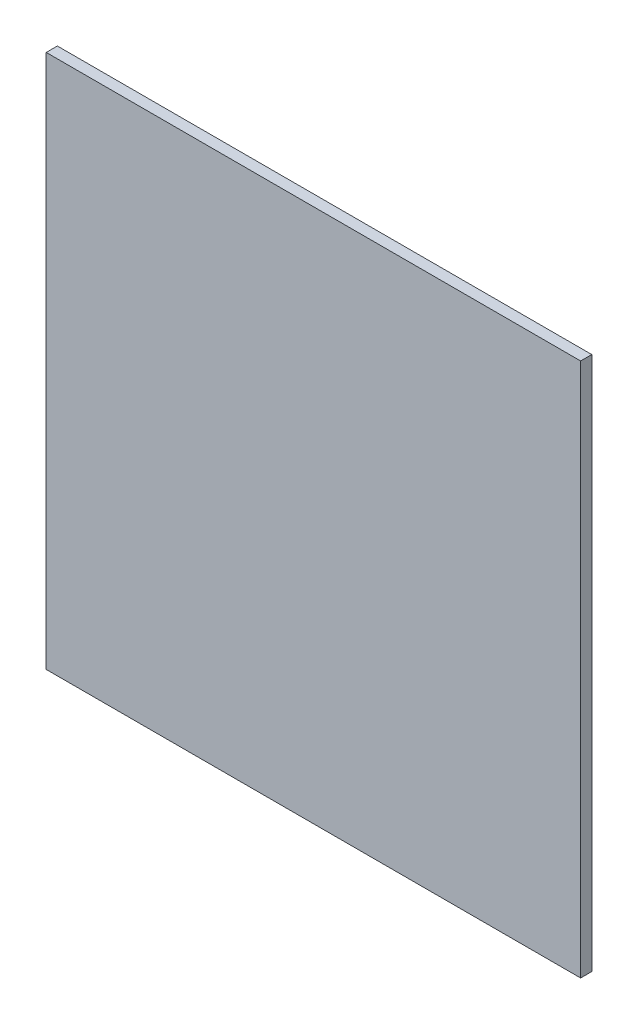
SolidWorks part; units mm, degrees
ref_plane "Front Plane" through (0, 0, 0) normal (0, 0, 1) x (1, 0, 0)
ref_plane "Top Plane" through (0, 0, 0) normal (0, 1, 0) x (1, 0, 0)
ref_plane "Right Plane" through (0, 0, 0) normal (1, 0, 0) x (0, 0, -1)
sketch "Sketch1" plane through (0, 0, 0) normal (0, 0, 1) x (1, 0, 0)
  line L1 (-304.8, -304.8) -> (304.8, -304.8)
  line L2 (-304.8, -304.8) -> (-304.8, 304.8)
  line L3 (-304.8, 304.8) -> (304.8, 304.8)
  line L4 (304.8, -304.8) -> (304.8, 304.8)
  line L5 (-304.8, -304.8) -> (304.8, 304.8) construction
  line L6 (-304.8, 304.8) -> (304.8, -304.8) construction
  point P0 (0, 0)
  dimension "D1" = 609.6
  dimension "D2" = 609.6
extrude "Boss-Extrude1" add sketch "Sketch1" along normal blind 12.7
